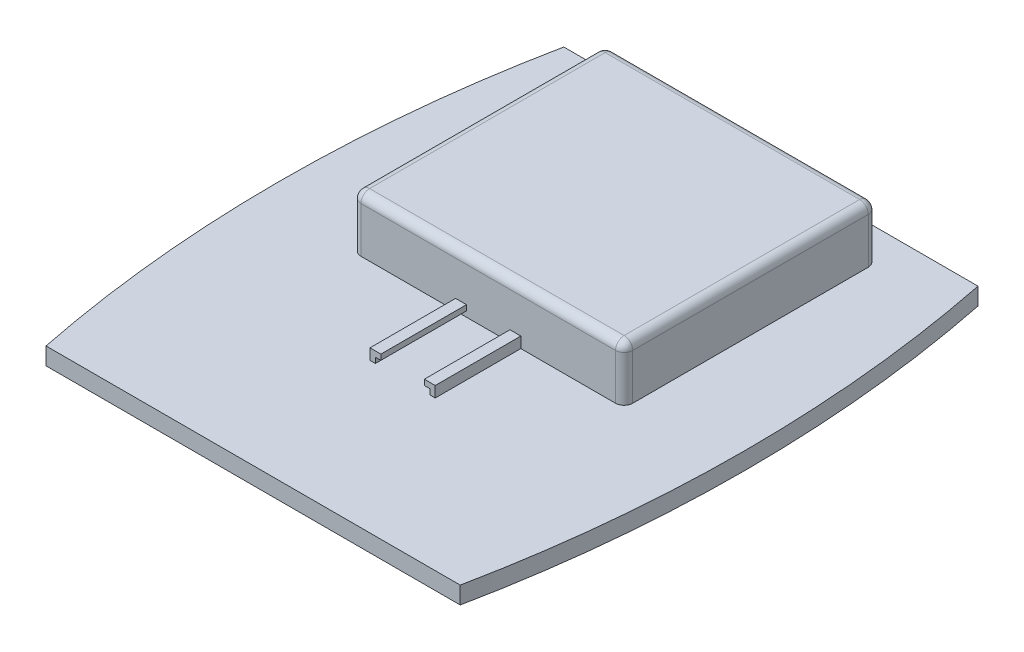
SolidWorks part; units mm, degrees
ref_plane "Front Plane" through (0, 0, 0) normal (0, 0, 1) x (1, 0, 0)
ref_plane "Top Plane" through (0, 0, 0) normal (0, 1, 0) x (1, 0, 0)
ref_plane "Right Plane" through (0, 0, 0) normal (1, 0, 0) x (0, 0, -1)
sketch "Sketch1" plane through (0, 0, 0) normal (0, 1, 0) x (1, 0, 0)
  line L1 (-76.2, 95.25) -> (76.2, 95.25)
  line L3 (-76.2, -95.25) -> (76.2, -95.25)
  line L5 (-76.2, 95.25) -> (76.2, -95.25) construction
  line L6 (-76.2, -95.25) -> (76.2, 95.25) construction
  arc A0 (-76.2, 95.25) -> (-76.2, -95.25) centre (395.2875, 0) ccw
  arc A1 (76.2, 95.25) -> (76.2, -95.25) centre (-395.2875, 0) cw
  point P0 (0, 0)
  point P8 (85.725, 0)
  point P11 (-85.725, 0)
  dimension "D1" = 152.4
  dimension "D2" = 190.5
  dimension "D3" = 171.45
extrude "Boss-Extrude1" add sketch "Sketch1" along normal blind 6.35
sketch "Sketch2" plane through (0, 6.35, 0) normal (0, 1, 0) x (1, 0, 0)
  line L0 (76.2, 95.25) -> (-76.2, 95.25) construction
  line L1 (-50, -8.75) -> (50, -8.75)
  line L2 (-50, -8.75) -> (-50, 84.25)
  line L3 (-50, 84.25) -> (50, 84.25)
  line L4 (50, -8.75) -> (50, 84.25)
  line L5 (-50, -8.75) -> (50, 84.25) construction
  line L6 (-50, 84.25) -> (50, -8.75) construction
  point P0 (0, 37.75)
  dimension "D1" = 93
  dimension "D2" = 100
  dimension "D3" = 11
extrude "Boss-Extrude2" add sketch "Sketch2" along normal blind 20
fillet "Fillet1" radius 3.175 8 edges at (0, 26.35, 8.75) (-50, 26.35, -37.75) (0, 26.35, -84.25) (50, 26.35, -37.75) (50, 16.35, -84.25) (-50, 16.35, -84.25) (50, 16.35, 8.75) (-50, 16.35, 8.75)
sketch "Sketch3" plane through (0, 0, 8.75) normal (0, 0, 1) x (1, 0, 0)
  line L0 (0, 0) -> (0, 41.6058) construction
  line L1 (-12, 6.35) -> (-12, 10.35)
  line L2 (-76.2, 6.35) -> (76.2, 6.35) construction
  line L3 (-12, 10.35) -> (-8, 10.35)
  line L4 (-8, 10.35) -> (-8, 8.35)
  line L5 (-8, 8.35) -> (-10, 8.35)
  line L6 (-10, 8.35) -> (-10, 6.35)
  line L7 (-46.825, 6.35) -> (46.825, 6.35) construction
  line L8 (-10, 6.35) -> (-12, 6.35)
  line L9 (10, 6.35) -> (12, 6.35)
  line L10 (10, 8.35) -> (10, 6.35)
  line L11 (8, 8.35) -> (10, 8.35)
  line L12 (8, 10.35) -> (8, 8.35)
  line L13 (12, 10.35) -> (8, 10.35)
  line L14 (12, 6.35) -> (12, 10.35)
  dimension "D1" = 4
  dimension "D2" = 2
  dimension "D3" = 20
  dimension "D4" = 24
  dimension "D5" = 4
extrude "Boss-Extrude3" add sketch "Sketch3" along normal blind 31.5
sketch "Sketch4" plane through (0, 0, 0) normal (0, -1, 0) x (1, 0, 0)
  line L0 (-85.725, 0) -> (85.725, 0)
  arc A0 (-76.2, 95.25) -> (-76.2, -95.25) centre (395.2875, 0) ccw construction
  arc A1 (76.2, -95.25) -> (76.2, 95.25) centre (-395.2875, 0) ccw construction
sketch "Sketch5" plane through (0, 0, 0) normal (0, -1, 0) x (1, 0, 0)
  line L0 (-63.5, -40.64) -> (-27.94, -40.64)
  line L5 (-17.78, -40.64) -> (17.78, -40.64)
  line L6 (-17.78, -40.64) -> (-17.78, -5.08)
  line L7 (-17.78, -5.08) -> (17.78, -5.08)
  line L8 (17.78, -40.64) -> (17.78, -5.08)
  line L9 (-17.78, -40.64) -> (17.78, -5.08) construction
  line L10 (-17.78, -5.08) -> (17.78, -40.64) construction
  line L11 (-63.5, -40.64) -> (-63.5, -5.08)
  line L12 (-63.5, -5.08) -> (-27.94, -5.08)
  line L13 (-27.94, -40.64) -> (-27.94, -5.08)
  line L14 (-63.5, -40.64) -> (-27.94, -5.08) construction
  line L15 (-63.5, -5.08) -> (-27.94, -40.64) construction
  line L16 (27.94, -40.64) -> (63.5, -40.64)
  line L17 (27.94, -40.64) -> (27.94, -5.08)
  line L18 (27.94, -5.08) -> (63.5, -5.08)
  line L19 (63.5, -40.64) -> (63.5, -5.08)
  line L20 (27.94, -40.64) -> (63.5, -5.08) construction
  line L21 (27.94, -5.08) -> (63.5, -40.64) construction
  point P0 (0, -22.86)
  point P5 (-45.72, -22.86)
  point P6 (-45.3907, -65.3627)
  point P11 (45.72, -22.86)
  point P16 (-49.022, -69.9399)
  point P17 (0, 0)
  point P19 (0, 0)
  point P20 (0, 0)
  dimension "D1" = 35.56
  dimension "D2" = 35.56
  dimension "D3" = 35.56
  dimension "D4" = 10.16
  dimension "D5" = 10.16
  dimension "D6" = 5.08
extrude "Cut-Extrude1" cut sketch "Sketch5" against normal blind 0.254
pattern_linear "LPattern1" count 3 spacing 45.72 along (0, 0, 1) of "Cut-Extrude1"
pattern_linear "LPattern2" count 2 spacing 45.72 along (0, 0, -1) of "Cut-Extrude1"
